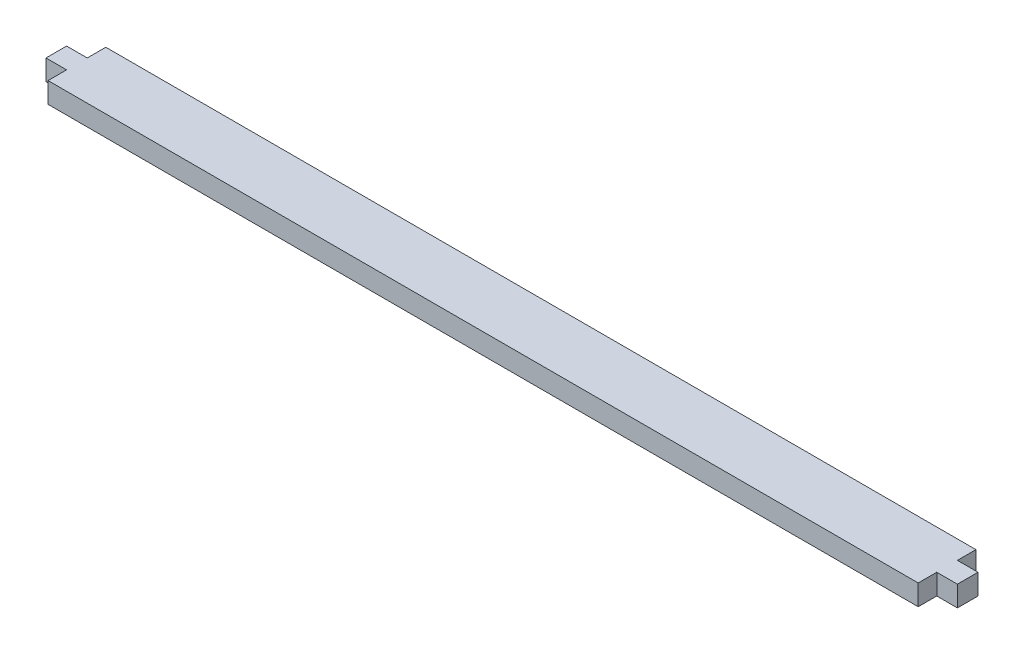
SolidWorks part; units mm, degrees
ref_plane "Alzado" through (0, 0, 0) normal (0, 0, 1) x (1, 0, 0)
ref_plane "Planta" through (0, 0, 0) normal (0, 1, 0) x (1, 0, 0)
ref_plane "Vista lateral" through (0, 0, 0) normal (1, 0, 0) x (0, 0, -1)
sketch "Croquis1" plane through (0, 0, 0) normal (0, 1, 0) x (1, 0, 0)
  line L0 (0, 14) -> (0, -14) construction
  line L1 (-221, 0) -> (221, 0) construction
  line L2 (-211, 14) -> (211, 14)
  line L3 (211, 14) -> (211, 5)
  line L4 (211, 5) -> (221, 5)
  line L5 (221, 5) -> (221, -5)
  line L6 (221, -5) -> (211, -5)
  line L7 (211, -5) -> (211, -14)
  line L8 (211, -14) -> (-211, -14)
  line L9 (-211, -14) -> (-211, -5)
  line L10 (-211, -5) -> (-221, -5)
  line L11 (-221, -5) -> (-221, 5)
  line L12 (-221, 5) -> (-211, 5)
  line L13 (-211, 5) -> (-211, 14)
  point P7 (0, 0)
  point P8 (0, 0)
  point P18 (-221, 0)
  point P21 (0, 14)
  dimension "D1" = 422
  dimension "D2" = 10
  dimension "D3" = 28
  dimension "D4" = 10
extrude "Saliente-Extruir1" add sketch "Croquis1" along normal blind 10
